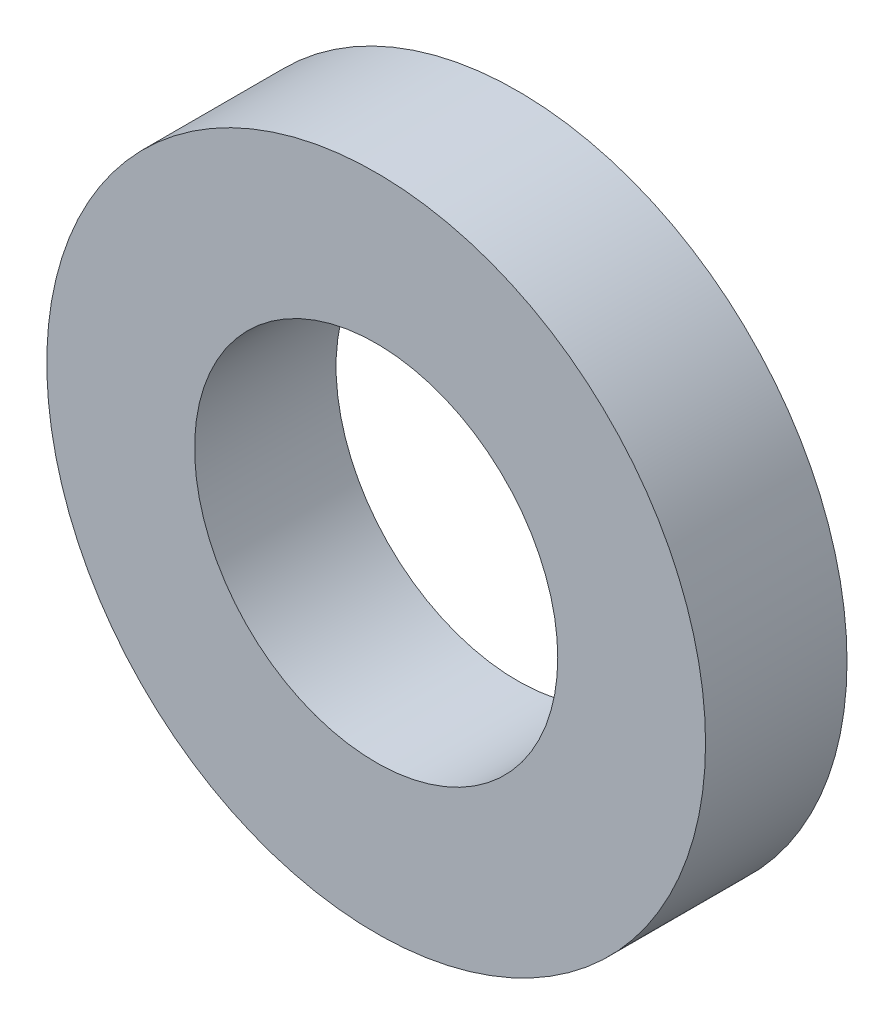
SolidWorks part; units mm, degrees
material "POLYURETHANE (11671)"
ref_plane "Front Plane" through (0, 0, 0) normal (0, 0, 1) x (1, 0, 0)
ref_plane "Top Plane" through (0, 0, 0) normal (0, 1, 0) x (1, 0, 0)
ref_plane "Right Plane" through (0, 0, 0) normal (1, 0, 0) x (0, 0, -1)
sketch "Sketch1" plane through (0, 0, 0) normal (0, 0, 1) x (1, 0, 0)
  circle A0 centre (0, 0) radius 2.1844
  circle A1 centre (0, 0) radius 3.9624
  dimension "ID" = 4.3688
  dimension "OD" = 7.9248
extrude "Extrude1" add sketch "Sketch1" against normal blind 1.7018
